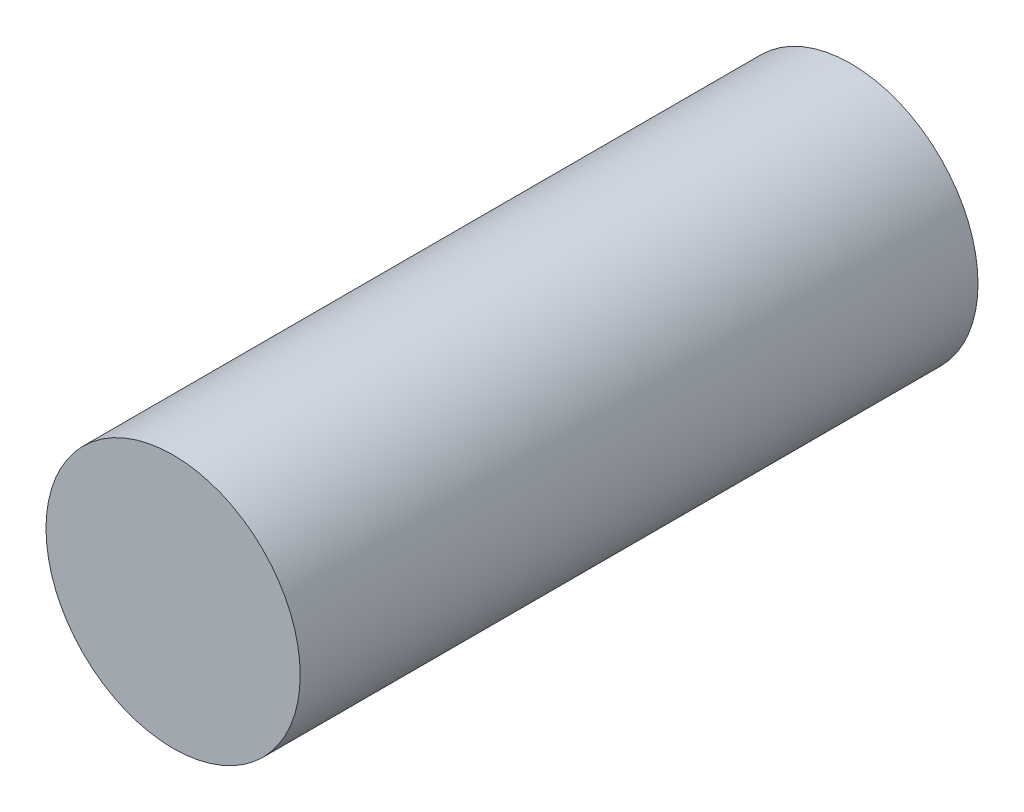
SolidWorks part; units mm, degrees
ref_plane "前视基准面" through (0, 0, 0) normal (0, 0, 1) x (1, 0, 0)
ref_plane "上视基准面" through (0, 0, 0) normal (0, 1, 0) x (1, 0, 0)
ref_plane "右视基准面" through (0, 0, 0) normal (1, 0, 0) x (0, 0, -1)
sketch "草图1" plane through (0, 0, 0) normal (0, 0, 1) x (1, 0, 0)
  circle A0 centre (0, 0) radius 1.5
extrude "凸台-拉伸1" add sketch "草图1" along normal blind 8
